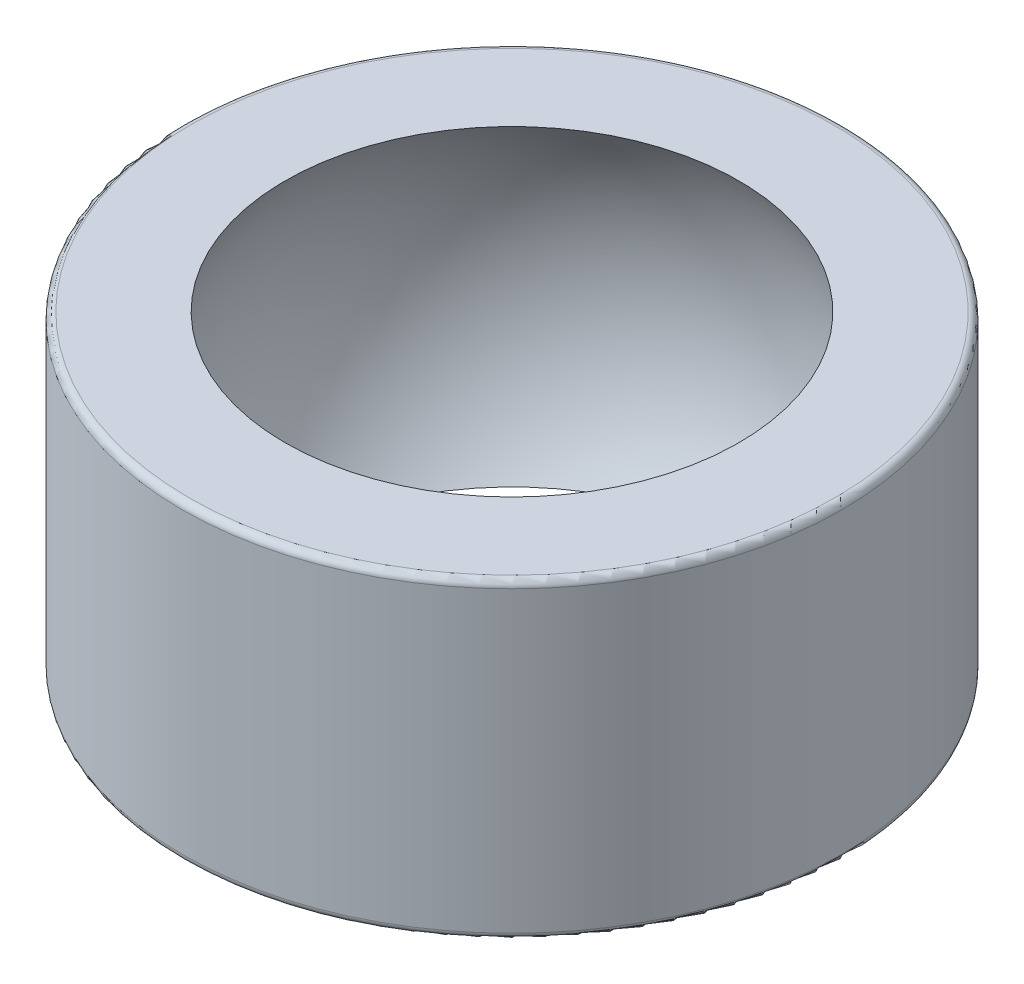
SolidWorks part; units mm, degrees
material "1.0545 (S355N)"
ref_plane "Płaszczyzna przednia" through (0, 0, 0) normal (0, 0, 1) x (1, 0, 0)
ref_plane "Płaszczyzna górna" through (0, 0, 0) normal (0, 1, 0) x (1, 0, 0)
ref_plane "Płaszczyzna prawa" through (0, 0, 0) normal (1, 0, 0) x (0, 0, -1)
sketch "Szkic1" plane through (0, 0, 0) normal (0, 1, 0) x (1, 0, 0)
  circle A0 centre (0, 0) radius 9.5
  dimension "d2" = 19
extrude "Dodanie-wyciągnięcie1" add sketch "Szkic1" along normal mid plane 9
sketch "Szkic3" plane through (0, 0, 0) normal (0, 0, 1) x (1, 0, 0)
  line L0 (0, -7.94) -> (0, 7.94)
  arc A0 (0, -7.94) -> (0, 7.94) centre (0, 0) ccw
  dimension "d3" = 15.88
revolve "Wycięcie-obrót1" cut sketch "Szkic3" angle 360 about L0
fillet "Zaokrąglenie1" radius 0.2 2 edges at (0, 4.5, 9.5) (0, -4.5, 9.5)
